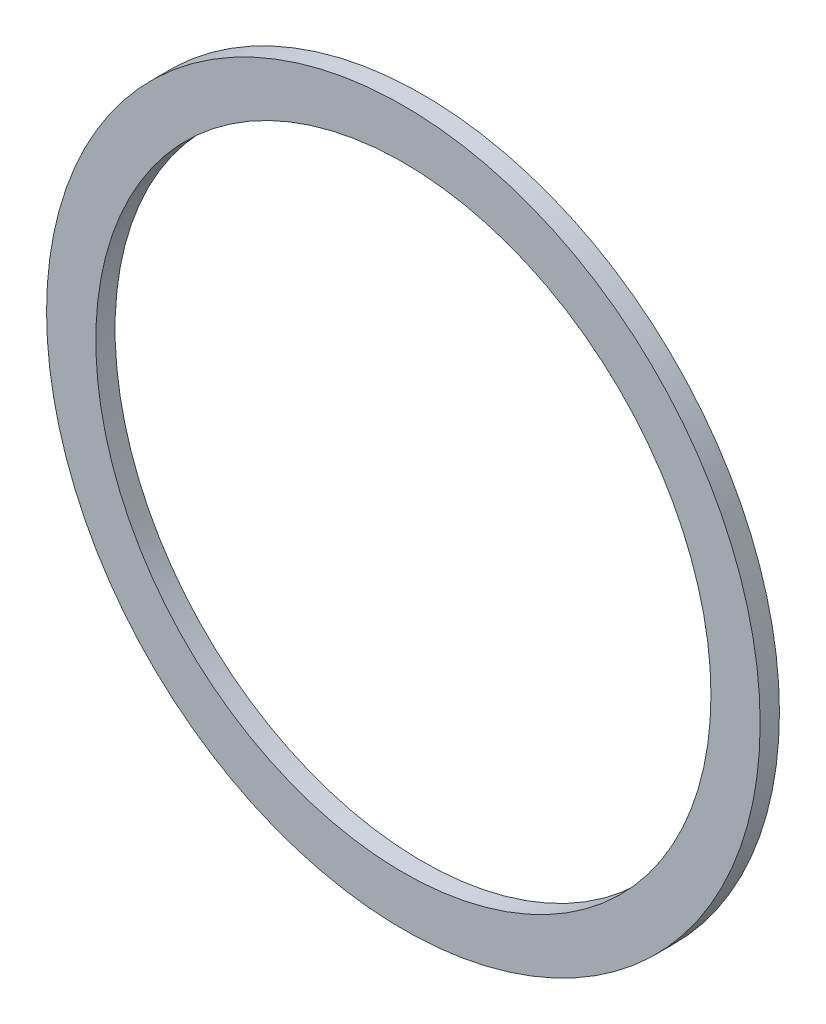
SolidWorks part; units mm, degrees
material "Silicon"
ref_plane "Front" through (0, 0, 0) normal (0, 0, 1) x (1, 0, 0)
ref_plane "Top" through (0, 0, 0) normal (0, 1, 0) x (1, 0, 0)
ref_plane "Right" through (0, 0, 0) normal (1, 0, 0) x (0, 0, -1)
sketch "Sketch1" plane through (0, 0, 0) normal (0, 0, 1) x (1, 0, 0)
  circle A0 centre (0, 0) radius 87
  circle A1 centre (0, 0) radius 75
extrude "Boss-Extrude1" add sketch "Sketch1" along normal blind 4.7
